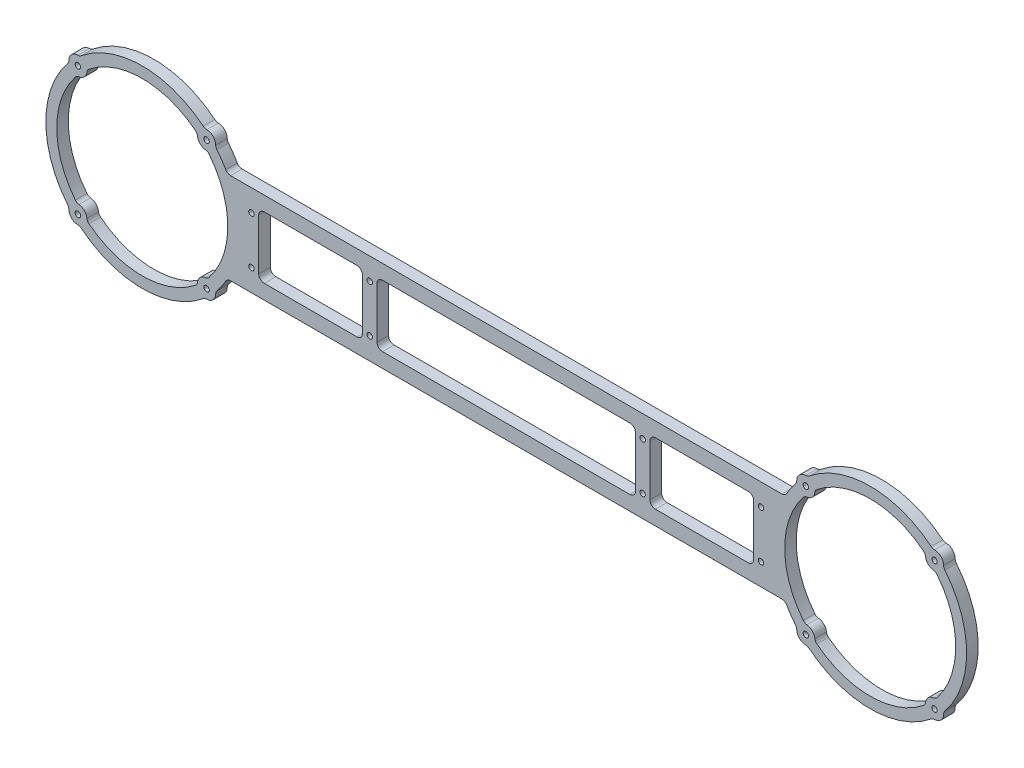
SolidWorks part; units mm, degrees
ref_plane "Front Plane" through (0, 0, 0) normal (0, 0, 1) x (1, 0, 0)
ref_plane "Top Plane" through (0, 0, 0) normal (0, 1, 0) x (1, 0, 0)
ref_plane "Right Plane" through (0, 0, 0) normal (1, 0, 0) x (0, 0, -1)
ref_plane "Plane1" through (0, 0, 0) normal (0, 0, -1) x (-1, 0, 0)
sketch "Sketch1" plane through (0, 0, 0) normal (0, 0, -1) x (-1, 0, 0)
  line L0 (136, 14) -> (136, -14)
  line L1 (133, -17) -> (82, -17)
  line L2 (79, -14) -> (79, 14)
  line L3 (82, 17) -> (133, 17)
  line L4 (71, 14) -> (71, -14)
  line L5 (68, -17) -> (-68, -17)
  line L6 (-71, -14) -> (-71, 14)
  line L7 (-68, 17) -> (68, 17)
  line L8 (-136, -14) -> (-136, 14)
  line L9 (-133, 17) -> (-82, 17)
  line L10 (-79, 14) -> (-79, -14)
  line L11 (-82, -17) -> (-133, -17)
  line L12 (151.5026, 25) -> (-151.5026, 25)
  line L13 (-151.5026, -25) -> (151.5026, -25)
  arc A0 (133, 17) -> (136, 14) centre (133, 14) cw
  arc A1 (136, -14) -> (133, -17) centre (133, -14) cw
  arc A2 (82, -17) -> (79, -14) centre (82, -14) cw
  arc A3 (79, 14) -> (82, 17) centre (82, 14) cw
  circle A4 centre (-235.3553, -35.3553) radius 1.5
  circle A5 centre (-235.3553, 35.3553) radius 1.5
  circle A6 centre (-164.6447, -35.3553) radius 1.5
  circle A7 centre (-164.6447, 35.3553) radius 1.5
  arc A8 (-163.2341, -29.2792) -> (-165.2298, -30.3897) centre (-165.5809, -27.4103) cw
  arc A9 (-165.2298, -30.3897) -> (-169.6103, -34.7702) centre (-164.6447, -35.3553) ccw
  arc A10 (-169.6103, -34.7702) -> (-170.7208, -36.7659) centre (-172.5897, -34.4191) cw
  arc A11 (-170.7208, -36.7659) -> (-229.2792, -36.7659) centre (-200, 0) cw
  arc A12 (-229.2792, -36.7659) -> (-230.3897, -34.7702) centre (-227.4103, -34.4191) cw
  arc A13 (-230.3897, -34.7702) -> (-234.7702, -30.3897) centre (-235.3553, -35.3553) ccw
  arc A14 (-234.7702, -30.3897) -> (-236.7659, -29.2792) centre (-234.4191, -27.4103) cw
  arc A15 (-236.7659, -29.2792) -> (-236.7659, 29.2792) centre (-200, 0) cw
  arc A16 (-236.7659, 29.2792) -> (-234.7702, 30.3897) centre (-234.4191, 27.4103) cw
  arc A17 (-234.7702, 30.3897) -> (-230.3897, 34.7702) centre (-235.3553, 35.3553) ccw
  arc A18 (-230.3897, 34.7702) -> (-229.2792, 36.7659) centre (-227.4103, 34.4191) cw
  arc A19 (-229.2792, 36.7659) -> (-170.7208, 36.7659) centre (-200, 0) cw
  arc A20 (-170.7208, 36.7659) -> (-169.6103, 34.7702) centre (-172.5897, 34.4191) cw
  arc A21 (-169.6103, 34.7702) -> (-165.2298, 30.3897) centre (-164.6447, 35.3553) ccw
  arc A22 (-165.2298, 30.3897) -> (-163.2341, 29.2792) centre (-165.5809, 27.4103) cw
  arc A23 (-163.2341, 29.2792) -> (-163.2341, -29.2792) centre (-200, 0) cw
  circle A24 centre (235.3553, -35.3553) radius 1.5
  circle A25 centre (235.3553, 35.3553) radius 1.5
  circle A26 centre (164.6447, -35.3553) radius 1.5
  circle A27 centre (164.6447, 35.3553) radius 1.5
  arc A28 (165.2298, -30.3897) -> (163.2341, -29.2792) centre (165.5809, -27.4103) cw
  arc A29 (163.2341, -29.2792) -> (163.2341, 29.2792) centre (200, 0) cw
  arc A30 (163.2341, 29.2792) -> (165.2298, 30.3897) centre (165.5809, 27.4103) cw
  arc A31 (165.2298, 30.3897) -> (169.6103, 34.7702) centre (164.6447, 35.3553) ccw
  arc A32 (169.6103, 34.7702) -> (170.7208, 36.7659) centre (172.5897, 34.4191) cw
  arc A33 (170.7208, 36.7659) -> (229.2792, 36.7659) centre (200, 0) cw
  arc A34 (229.2792, 36.7659) -> (230.3897, 34.7702) centre (227.4103, 34.4191) cw
  arc A35 (230.3897, 34.7702) -> (234.7702, 30.3897) centre (235.3553, 35.3553) ccw
  arc A36 (234.7702, 30.3897) -> (236.7659, 29.2792) centre (234.4191, 27.4103) cw
  arc A37 (236.7659, 29.2792) -> (236.7659, -29.2792) centre (200, 0) cw
  arc A38 (236.7659, -29.2792) -> (234.7702, -30.3897) centre (234.4191, -27.4103) cw
  arc A39 (234.7702, -30.3897) -> (230.3897, -34.7702) centre (235.3553, -35.3553) ccw
  arc A40 (230.3897, -34.7702) -> (229.2792, -36.7659) centre (227.4103, -34.4191) cw
  arc A41 (229.2792, -36.7659) -> (170.7208, -36.7659) centre (200, 0) cw
  arc A42 (170.7208, -36.7659) -> (169.6103, -34.7702) centre (172.5897, -34.4191) cw
  arc A43 (169.6103, -34.7702) -> (165.2298, -30.3897) centre (164.6447, -35.3553) ccw
  circle A44 centre (75, 13) radius 1.5
  circle A45 centre (75, -13) radius 1.5
  circle A46 centre (-75, -13) radius 1.5
  circle A47 centre (-75, 13) radius 1.5
  circle A48 centre (140, 13) radius 1.5
  circle A49 centre (140, -13) radius 1.5
  circle A50 centre (-140, -13) radius 1.5
  circle A51 centre (-140, 13) radius 1.5
  arc A52 (68, 17) -> (71, 14) centre (68, 14) cw
  arc A53 (71, -14) -> (68, -17) centre (68, -14) cw
  arc A54 (-68, -17) -> (-71, -14) centre (-68, -14) cw
  arc A55 (-71, 14) -> (-68, 17) centre (-68, 14) cw
  arc A56 (-133, -17) -> (-136, -14) centre (-133, -14) cw
  arc A57 (-136, 14) -> (-133, 17) centre (-133, 14) cw
  arc A58 (-82, 17) -> (-79, 14) centre (-82, 14) cw
  arc A59 (-79, -14) -> (-82, -17) centre (-82, -14) cw
  arc A60 (241.0323, 33.5463) -> (240.355, 35.4115) centre (243.3548, 35.4451) cw
  arc A61 (240.355, 35.4115) -> (235.4115, 40.355) centre (235.3553, 35.3553) ccw
  arc A62 (235.4115, 40.355) -> (233.5463, 41.0323) centre (235.4451, 43.3548) cw
  arc A63 (233.5463, 41.0323) -> (166.4537, 41.0323) centre (200, 0) ccw
  arc A64 (166.4537, 41.0323) -> (164.5885, 40.355) centre (164.5549, 43.3548) cw
  arc A65 (164.5885, 40.355) -> (159.645, 35.4115) centre (164.6447, 35.3553) ccw
  arc A66 (159.645, 35.4115) -> (158.9677, 33.5463) centre (156.6452, 35.4451) cw
  arc A67 (158.9677, 33.5463) -> (154.1007, 26.5) centre (200, 0) ccw
  arc A68 (154.1007, 26.5) -> (151.5026, 25) centre (151.5026, 28) cw
  arc A69 (-151.5026, 25) -> (-154.1007, 26.5) centre (-151.5026, 28) cw
  arc A70 (-154.1007, 26.5) -> (-158.9677, 33.5463) centre (-200, 0) ccw
  arc A71 (-158.9677, 33.5463) -> (-159.645, 35.4115) centre (-156.6452, 35.4451) cw
  arc A72 (-159.645, 35.4115) -> (-164.5885, 40.355) centre (-164.6447, 35.3553) ccw
  arc A73 (-164.5885, 40.355) -> (-166.4537, 41.0323) centre (-164.5549, 43.3548) cw
  arc A74 (-166.4537, 41.0323) -> (-233.5463, 41.0323) centre (-200, 0) ccw
  arc A75 (-233.5463, 41.0323) -> (-235.4115, 40.355) centre (-235.4451, 43.3548) cw
  arc A76 (-235.4115, 40.355) -> (-240.355, 35.4115) centre (-235.3553, 35.3553) ccw
  arc A77 (-240.355, 35.4115) -> (-241.0323, 33.5463) centre (-243.3548, 35.4451) cw
  arc A78 (-241.0323, 33.5463) -> (-241.0323, -33.5463) centre (-200, 0) ccw
  arc A79 (-241.0323, -33.5463) -> (-240.355, -35.4115) centre (-243.3548, -35.4451) cw
  arc A80 (-240.355, -35.4115) -> (-235.4115, -40.355) centre (-235.3553, -35.3553) ccw
  arc A81 (-235.4115, -40.355) -> (-233.5463, -41.0323) centre (-235.4451, -43.3548) cw
  arc A82 (-233.5463, -41.0323) -> (-166.4537, -41.0323) centre (-200, 0) ccw
  arc A83 (-166.4537, -41.0323) -> (-164.5885, -40.355) centre (-164.5549, -43.3548) cw
  arc A84 (-164.5885, -40.355) -> (-159.645, -35.4115) centre (-164.6447, -35.3553) ccw
  arc A85 (-159.645, -35.4115) -> (-158.9677, -33.5463) centre (-156.6452, -35.4451) cw
  arc A86 (-158.9677, -33.5463) -> (-154.1007, -26.5) centre (-200, 0) ccw
  arc A87 (-154.1007, -26.5) -> (-151.5026, -25) centre (-151.5026, -28) cw
  arc A88 (151.5026, -25) -> (154.1007, -26.5) centre (151.5026, -28) cw
  arc A89 (154.1007, -26.5) -> (158.9677, -33.5463) centre (200, 0) ccw
  arc A90 (158.9677, -33.5463) -> (159.645, -35.4115) centre (156.6452, -35.4451) cw
  arc A91 (159.645, -35.4115) -> (164.5885, -40.355) centre (164.6447, -35.3553) ccw
  arc A92 (164.5885, -40.355) -> (166.4537, -41.0323) centre (164.5549, -43.3548) cw
  arc A93 (166.4537, -41.0323) -> (233.5463, -41.0323) centre (200, 0) ccw
  arc A94 (233.5463, -41.0323) -> (235.4115, -40.355) centre (235.4451, -43.3548) cw
  arc A95 (235.4115, -40.355) -> (240.355, -35.4115) centre (235.3553, -35.3553) ccw
  arc A96 (240.355, -35.4115) -> (241.0323, -33.5463) centre (243.3548, -35.4451) cw
  arc A97 (241.0323, -33.5463) -> (241.0323, 33.5463) centre (200, 0) ccw
extrude "Boss-Extrude1" add sketch "Sketch1" against normal blind 6.35
